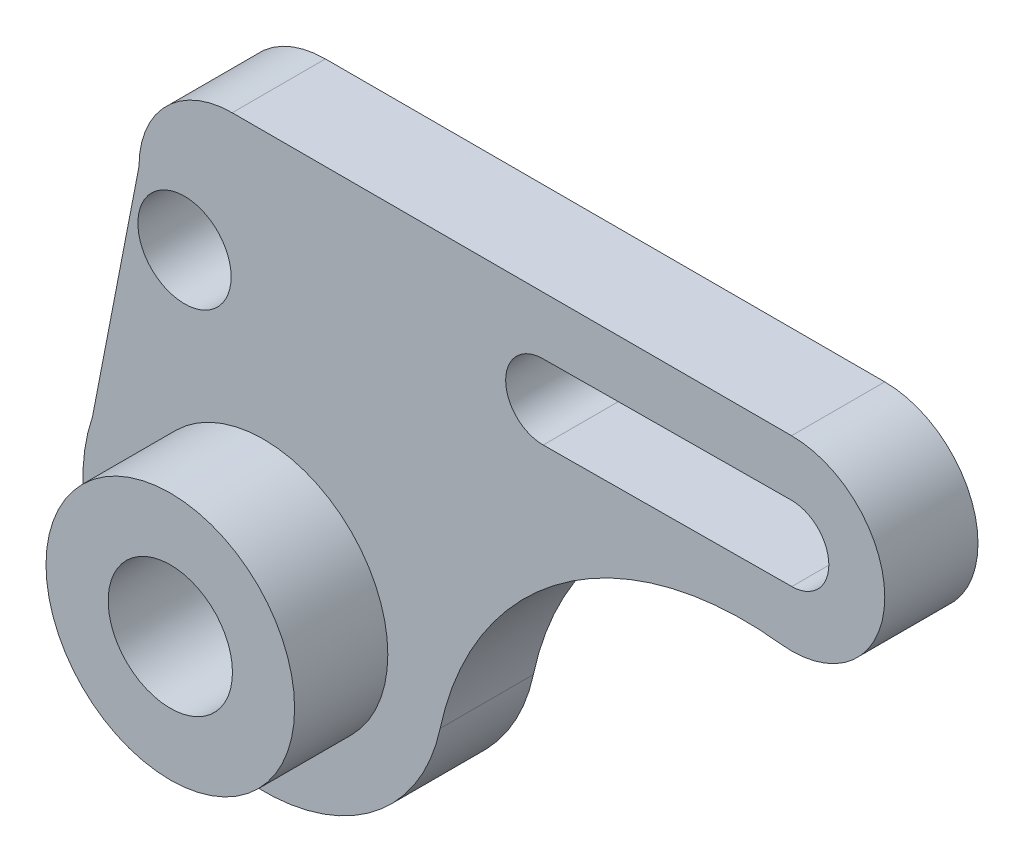
SolidWorks part; units mm, degrees
ref_plane "Front Plane" through (0, 0, 0) normal (0, 0, 1) x (1, 0, 0)
ref_plane "Top Plane" through (0, 0, 0) normal (0, 1, 0) x (1, 0, 0)
ref_plane "Right Plane" through (0, 0, 0) normal (1, 0, 0) x (0, 0, -1)
sketch "Sketch1" plane through (0, 0, 0) normal (0, 0, 1) x (1, 0, 0)
  line L0 (0, 36.1937) -> (0, -37.5188) construction
  line L1 (1246.3369, 5.8132) -> (122.6902, 5.8132) construction
  line L2 (84.9581, 74.4224) -> (84.9581, 41.9633) construction
  line L3 (51.3498, 47.9635) -> (134.2018, 47.9635) construction
  line L4 (44.9581, 74.4224) -> (44.9581, 20.9463) construction
  line L5 (44.9581, 47.6844) -> (84.9581, 47.9635) construction
  line L6 (44.9163, 53.6842) -> (84.9163, 53.9633)
  line L7 (45, 41.6845) -> (85, 41.9636)
  line L8 (-5.0419, 85.7599) -> (-5.0419, 29.5733) construction
  line L9 (84.9581, 5.8132) -> (-37.1502, 5.8132) construction
  line L10 (-5.0419, 62.9635) -> (84.9581, 62.9635)
  line L11 (-20.0419, 47.9635) -> (-28.802, 2.7546)
  line L12 (84.9581, 32.9635) -> (84.9581, 5.8132) construction
  arc A1 (44.9163, 53.6842) -> (45, 41.6845) centre (44.9581, 47.6844) ccw
  arc A2 (85, 41.9636) -> (84.9163, 53.9633) centre (84.9581, 47.9635) ccw
  arc A6 (69.9581, 47.9635) -> (69.9585, 47.8588) centre (84.9581, 47.9635) ccw
  arc A7 (83.1926, 33.0678) -> (84.9581, 62.9635) centre (84.9581, 47.9635) ccw
  arc A8 (-27.5272, 9.3334) -> (28.4199, -6.0969) centre (0, 0) ccw
  arc A9 (-5.0419, 62.9635) -> (-20.0419, 47.9635) centre (-5.0419, 47.9635) ccw
  arc A10 (84.9581, 32.8265) -> (28.4199, -6.0969) centre (77.3075, -16.5847) ccw
  point P15 (64.9581, 47.8239)
  dimension "D1" = 100
  dimension "D4" = 6
  dimension "D6" = 30
  dimension "D3" = 40
  dimension "D5" = 50
extrude "Boss-Extrude2" add sketch "Sketch1" along normal blind 15
sketch "Sketch2" plane through (0, 0, 15) normal (0, 0, 1) x (1, 0, 0)
  line L0 (0, 40.1898) -> (0, -40.1898)
  line L1 (-19.8302, 0) -> (38.7472, 0)
  arc A0 (-27.5272, 9.3334) -> (28.4199, -6.0969) centre (0, 0) ccw construction
  arc A1 (-27.5272, 9.3334) -> (28.4199, -6.0969) centre (0, 0) ccw
  circle A2 centre (0, 0) radius 20
  dimension "D1" = 40
extrude "Boss-Extrude3" add sketch "Sketch2" along normal blind 35 contours A2
sketch "Sketch3" plane through (0, 0, 50) normal (0, 0, 1) x (1, 0, 0)
  line L0 (0, 36.6718) -> (0, -38.1582)
  line L1 (-37.268, 0) -> (41.1173, 0)
  line L2 (-7.6407, 59.3847) -> (-7.6407, 20.6153)
  line L3 (-37.268, 40) -> (23.341, 40)
  arc A0 (-27.5272, 9.3334) -> (28.4199, -6.0969) centre (0, 0) ccw construction
  arc A1 (-27.5272, 9.3334) -> (28.4199, -6.0969) centre (0, 0) ccw
  circle A2 centre (0, 0) radius 10
  circle A3 centre (-7.6407, 40) radius 7.5
  point P15 (-7.6407, 40)
  dimension "D1" = 20
  dimension "D3" = 15
  dimension "D2" = 40
extrude "Cut-Extrude2" cut sketch "Sketch3" against normal through all contours A2
sketch "Sketch6" plane through (0, 0, 50) normal (0, 0, 1) x (1, 0, 0)
  circle A0 centre (0, 0) radius 20 construction
  circle A1 centre (0, 0) radius 20
extrude "Cut-Extrude3" cut sketch "Sketch6" against normal blind 20
sketch "Sketch7" plane through (0, 0, 30) normal (0, 0, 1) x (1, 0, 0)
  line L0 (0, 0) -> (-45.5316, 0)
  line L1 (-45.5316, 40) -> (20.0983, 40)
  line L2 (-12.7166, 56.5469) -> (-12.7166, 27.2085)
  circle A0 centre (-12.7166, 40) radius 7.5
  dimension "D2" = 15
  dimension "D1" = 40
extrude "Cut-Extrude4" cut sketch "Sketch7" against normal through all contours A0
